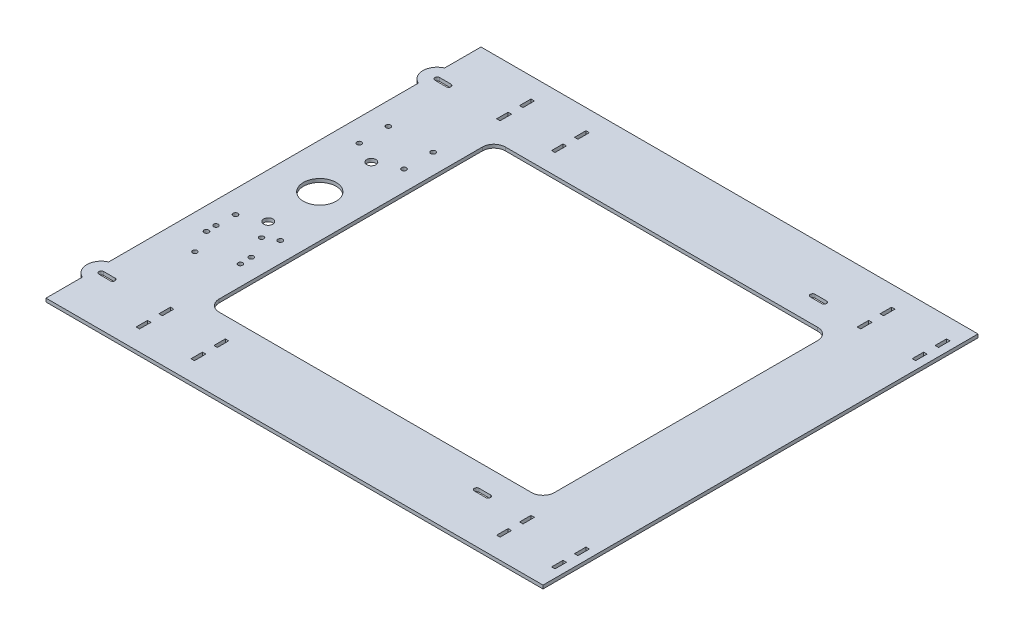
SolidWorks part; units mm, degrees
material "PC High Viscosity"
ref_plane "Front Plane" through (0, 0, 0) normal (0, 0, 1) x (1, 0, 0)
ref_plane "Top Plane" through (0, 0, 0) normal (0, 1, 0) x (1, 0, 0)
ref_plane "Right Plane" through (0, 0, 0) normal (1, 0, 0) x (0, 0, -1)
sketch "Sketch1" plane through (0, 0, 0) normal (0, 1, 0) x (1, 0, 0)
  line L1 (217.09, -190) -> (-217.09, -190)
  line L2 (217.09, -190) -> (217.09, 190)
  line L3 (217.09, 190) -> (-217.09, 190)
  line L4 (-217.09, -190) -> (-217.09, 190)
  line L5 (217.09, -190) -> (-217.09, 190) construction
  line L6 (217.09, 190) -> (-217.09, -190) construction
  point P0 (0, 0)
  dimension "D1" = 434.18
  dimension "D2" = 380
extrude "Boss-Extrude1" add sketch "Sketch1" along normal blind 3 contours L4 L3 L2 L1
sketch "Sketch2" plane through (0, 3, 0) normal (0, 1, 0) x (1, 0, 0)
  line L0 (217.09, 0) -> (-217.09, 0) construction
  line L1 (217.09, -190) -> (217.09, 190) construction
  line L2 (-217.09, 190) -> (-217.09, -190) construction
  line L4 (-97.91, -125) -> (152.09, -125)
  line L5 (-97.91, -125) -> (-97.91, 125)
  line L6 (-97.91, 125) -> (152.09, 125)
  line L7 (152.09, -125) -> (152.09, 125)
  line L8 (-97.91, -125) -> (152.09, 125) construction
  line L9 (-97.91, 125) -> (152.09, -125) construction
  line L10 (152.09, 125) -> (217.09, 125) construction
  line L11 (152.09, 125) -> (152.09, 190) construction
  line L12 (152.09, 190) -> (217.09, 190) construction
  line L13 (217.09, 125) -> (217.09, 190) construction
  point P6 (27.09, 0)
  dimension "D1" = 250
  dimension "D2" = 250
extrude "Cut-Extrude1" cut sketch "Sketch2" against normal through all
sketch "Sketch3" plane through (0, 3, 0) normal (0, 1, 0) x (1, 0, 0)
  line L0 (160.59, -152.5) -> (160.59, -162.5) construction
  line L1 (159.09, -152.5) -> (162.09, -152.5)
  line L2 (159.09, -152.5) -> (159.09, -142.5)
  line L3 (159.09, -142.5) -> (162.09, -142.5)
  line L4 (162.09, -152.5) -> (162.09, -142.5)
  line L5 (159.09, -152.5) -> (162.09, -142.5) construction
  line L6 (159.09, -142.5) -> (162.09, -152.5) construction
  line L7 (159.09, -172.5) -> (162.09, -172.5)
  line L8 (159.09, -172.5) -> (159.09, -162.5)
  line L9 (159.09, -162.5) -> (162.09, -162.5)
  line L10 (162.09, -172.5) -> (162.09, -162.5)
  line L11 (159.09, -172.5) -> (162.09, -162.5) construction
  line L12 (159.09, -162.5) -> (162.09, -172.5) construction
  line L13 (210.09, -152.5) -> (207.09, -152.5)
  line L14 (210.09, -152.5) -> (210.09, -142.5)
  line L15 (210.09, -142.5) -> (207.09, -142.5)
  line L16 (207.09, -152.5) -> (207.09, -142.5)
  line L17 (210.09, -152.5) -> (207.09, -142.5) construction
  line L18 (210.09, -142.5) -> (207.09, -152.5) construction
  line L19 (210.09, -172.5) -> (207.09, -172.5)
  line L20 (210.09, -172.5) -> (210.09, -162.5)
  line L21 (210.09, -162.5) -> (207.09, -162.5)
  line L22 (207.09, -172.5) -> (207.09, -162.5)
  line L23 (210.09, -172.5) -> (207.09, -162.5) construction
  line L24 (210.09, -162.5) -> (207.09, -172.5) construction
  line L25 (160.59, -167.5) -> (208.59, -167.5) construction
  line L26 (160.59, -167.5) -> (160.59, -147.5) construction
  line L27 (160.59, -147.5) -> (208.59, -147.5) construction
  line L28 (208.59, -167.5) -> (208.59, -147.5) construction
  line L29 (160.59, -167.5) -> (208.59, -147.5) construction
  line L30 (160.59, -147.5) -> (208.59, -167.5) construction
  line L31 (27.09, 125) -> (27.09, -125) construction
  line L32 (-130.41, 157.5) -> (184.59, 157.5) construction
  line L33 (-130.41, 157.5) -> (-130.41, -157.5) construction
  line L34 (-130.41, -157.5) -> (184.59, -157.5) construction
  line L35 (184.59, 157.5) -> (184.59, -157.5) construction
  line L36 (-130.41, 157.5) -> (184.59, -157.5) construction
  line L37 (-130.41, -157.5) -> (184.59, 157.5) construction
  line L38 (152.09, 125) -> (-97.91, 125) construction
  line L39 (-97.91, -125) -> (152.09, -125) construction
  line L40 (184.59, 0) -> (-130.41, 0) construction
  line L41 (-155.91, -142.5) -> (-152.91, -152.5) construction
  line L42 (-155.91, -152.5) -> (-152.91, -142.5) construction
  line L43 (-152.91, -152.5) -> (-152.91, -142.5)
  line L44 (-155.91, -142.5) -> (-152.91, -142.5)
  line L45 (-155.91, -152.5) -> (-155.91, -142.5)
  line L46 (-155.91, -152.5) -> (-152.91, -152.5)
  line L47 (-155.91, -162.5) -> (-152.91, -172.5) construction
  line L48 (-155.91, -172.5) -> (-152.91, -162.5) construction
  line L49 (-152.91, -172.5) -> (-152.91, -162.5)
  line L50 (-155.91, -162.5) -> (-152.91, -162.5)
  line L51 (-155.91, -172.5) -> (-155.91, -162.5)
  line L52 (-155.91, -172.5) -> (-152.91, -172.5)
  line L53 (-104.91, -162.5) -> (-107.91, -172.5) construction
  line L54 (-104.91, -172.5) -> (-107.91, -162.5) construction
  line L55 (-107.91, -172.5) -> (-107.91, -162.5)
  line L56 (-104.91, -162.5) -> (-107.91, -162.5)
  line L57 (-104.91, -172.5) -> (-104.91, -162.5)
  line L58 (-104.91, -172.5) -> (-107.91, -172.5)
  line L59 (-104.91, -142.5) -> (-107.91, -152.5) construction
  line L60 (-104.91, -152.5) -> (-107.91, -142.5) construction
  line L61 (-107.91, -152.5) -> (-107.91, -142.5)
  line L62 (-104.91, -142.5) -> (-107.91, -142.5)
  line L63 (-104.91, -152.5) -> (-104.91, -142.5)
  line L64 (-104.91, -152.5) -> (-107.91, -152.5)
  line L65 (210.09, 142.5) -> (207.09, 152.5) construction
  line L66 (210.09, 152.5) -> (207.09, 142.5) construction
  line L67 (207.09, 152.5) -> (207.09, 142.5)
  line L68 (210.09, 142.5) -> (207.09, 142.5)
  line L69 (210.09, 152.5) -> (210.09, 142.5)
  line L70 (210.09, 152.5) -> (207.09, 152.5)
  line L71 (210.09, 162.5) -> (207.09, 172.5) construction
  line L72 (210.09, 172.5) -> (207.09, 162.5) construction
  line L73 (207.09, 172.5) -> (207.09, 162.5)
  line L74 (210.09, 162.5) -> (207.09, 162.5)
  line L75 (210.09, 172.5) -> (210.09, 162.5)
  line L76 (210.09, 172.5) -> (207.09, 172.5)
  line L77 (159.09, 162.5) -> (162.09, 172.5) construction
  line L78 (159.09, 172.5) -> (162.09, 162.5) construction
  line L79 (162.09, 172.5) -> (162.09, 162.5)
  line L80 (159.09, 162.5) -> (162.09, 162.5)
  line L81 (159.09, 172.5) -> (159.09, 162.5)
  line L82 (159.09, 172.5) -> (162.09, 172.5)
  line L83 (159.09, 142.5) -> (162.09, 152.5) construction
  line L84 (159.09, 152.5) -> (162.09, 142.5) construction
  line L85 (162.09, 152.5) -> (162.09, 142.5)
  line L86 (159.09, 142.5) -> (162.09, 142.5)
  line L87 (159.09, 152.5) -> (159.09, 142.5)
  line L88 (159.09, 152.5) -> (162.09, 152.5)
  line L89 (-130.41, -157.5) -> (184.59, 157.5) construction
  line L90 (-104.91, 152.5) -> (-107.91, 142.5) construction
  line L91 (-104.91, 142.5) -> (-107.91, 152.5) construction
  line L92 (-104.91, 172.5) -> (-107.91, 162.5) construction
  line L93 (-104.91, 162.5) -> (-107.91, 172.5) construction
  line L94 (-104.91, 152.5) -> (-107.91, 152.5)
  line L95 (-104.91, 152.5) -> (-104.91, 142.5)
  line L96 (-104.91, 142.5) -> (-107.91, 142.5)
  line L97 (-107.91, 152.5) -> (-107.91, 142.5)
  line L98 (-104.91, 172.5) -> (-107.91, 172.5)
  line L99 (-104.91, 172.5) -> (-104.91, 162.5)
  line L100 (-104.91, 162.5) -> (-107.91, 162.5)
  line L101 (-107.91, 172.5) -> (-107.91, 162.5)
  line L102 (-155.91, 172.5) -> (-152.91, 162.5) construction
  line L103 (-155.91, 162.5) -> (-152.91, 172.5) construction
  line L104 (-155.91, 152.5) -> (-152.91, 142.5) construction
  line L105 (-155.91, 142.5) -> (-152.91, 152.5) construction
  line L106 (-155.91, 172.5) -> (-152.91, 172.5)
  line L107 (-155.91, 172.5) -> (-155.91, 162.5)
  line L108 (-155.91, 162.5) -> (-152.91, 162.5)
  line L109 (-152.91, 172.5) -> (-152.91, 162.5)
  line L110 (-155.91, 152.5) -> (-152.91, 152.5)
  line L111 (-155.91, 152.5) -> (-155.91, 142.5)
  line L112 (-155.91, 142.5) -> (-152.91, 142.5)
  line L113 (-152.91, 152.5) -> (-152.91, 142.5)
  line L114 (-217.09, -190) -> (217.09, -190) construction
  line L115 (152.09, -125) -> (152.09, 125) construction
  point P0 (160.59, -147.5)
  point P5 (160.59, -167.5)
  point P10 (208.59, -147.5)
  point P15 (208.59, -167.5)
  point P20 (184.59, -157.5)
  point P27 (27.09, 0)
  point P44 (-154.41, -147.5)
  point P49 (-154.41, -167.5)
  point P54 (-106.41, -167.5)
  point P59 (-106.41, -147.5)
  point P64 (208.59, 147.5)
  point P69 (208.59, 167.5)
  point P74 (160.59, 167.5)
  point P79 (160.59, 147.5)
  point P88 (-106.41, 147.5)
  point P89 (-106.41, 167.5)
  point P98 (-154.41, 167.5)
  point P99 (-154.41, 147.5)
  dimension "D1" = 3
  dimension "D2" = 45
  dimension "D3" = 10
  dimension "D4" = 32.5
  dimension "D5" = 32.5
extrude "Cut-Extrude2" cut sketch "Sketch3" against normal through all
sketch "Sketch6" plane through (0, 3, 0) normal (0, 1, 0) x (1, 0, 0)
  line L0 (-197.475, 10) -> (-158.345, 10) construction
  line L1 (-97.91, 125) -> (-97.91, -125) construction
  line L2 (-158.345, -44.0505) -> (-197.475, -44.0505) construction
  line L3 (-168.6822, -50.1326) -> (-158.0266, -79.2438) construction
  line L4 (-168.6822, -50.1326) -> (-197.7934, -60.7882) construction
  line L5 (-197.7934, -60.7882) -> (-187.1378, -89.8994) construction
  line L6 (-158.0266, -79.2438) -> (-187.1378, -89.8994) construction
  line L7 (-168.6822, -50.1326) -> (-187.1378, -89.8994) construction
  line L8 (-197.7934, -60.7882) -> (-158.0266, -79.2438) construction
  line L9 (-158.345, -44.0505) -> (-158.345, 64.0505) construction
  line L10 (-158.345, 64.0505) -> (-197.475, 64.0505) construction
  line L11 (-197.475, -44.0505) -> (-197.475, 64.0505) construction
  line L12 (-158.345, -44.0505) -> (-197.475, 64.0505) construction
  line L13 (-158.345, 64.0505) -> (-197.475, -44.0505) construction
  line L14 (-197.475, 64.0505) -> (-158.345, 64.0505) construction
  line L15 (-197.475, 64.0505) -> (-197.475, 89.4505) construction
  line L16 (-197.475, 89.4505) -> (-158.345, 89.4505) construction
  line L17 (-158.345, 64.0505) -> (-158.345, 89.4505) construction
  line L18 (-217.09, 10) -> (-97.91, 10) construction
  line L20 (-217.09, 190) -> (-217.09, -190) construction
  line L21 (-97.91, 125) -> (-97.91, -125) construction
  circle A0 centre (-177.91, 10) radius 14.2875
  circle A1 centre (-197.7934, -60.7882) radius 2
  circle A2 centre (-187.1378, -89.8994) radius 2
  circle A3 centre (-158.0266, -79.2438) radius 2
  circle A4 centre (-168.6822, -50.1326) radius 2
  circle A5 centre (-158.345, 64.0505) radius 2.0833
  circle A6 centre (-197.475, 64.0505) radius 2.0833
  circle A7 centre (-197.475, -44.0505) radius 2.0833
  circle A8 centre (-158.345, -44.0505) radius 2.0833
  circle A9 centre (-197.475, 89.4505) radius 2.0833
  circle A10 centre (-158.345, 89.4505) radius 2.0833
  circle A11 centre (-158.345, -69.4505) radius 2.0833
  circle A12 centre (-197.475, -69.4505) radius 2.0833
  circle A13 centre (-177.91, -35) radius 4
  circle A14 centre (-177.91, 55) radius 4
  point P6 (-177.91, -70.016)
  dimension "D1" = 28.575
  dimension "D2" = 80
  dimension "D3" = 4
  dimension "D9" = 4.1667
  dimension "D11" = 8
  dimension "D12" = 90
  dimension "D4" = 31
  dimension "D5" = 80.016
  dimension "D6" = 10
  dimension "D7" = 108.101
  dimension "D8" = 39.13
  dimension "D10" = 25.4
extrude "Cut-Extrude3" cut sketch "Sketch6" against normal through all
sketch "Sketch7" plane through (0, 3, 0) normal (0, 1, 0) x (1, 0, 0)
  line L0 (-97.91, -125) -> (152.09, -125) construction
  line L1 (-57.5273, -125) -> (-140.8107, -125)
  line L2 (-57.5273, -125) -> (-57.5273, 125)
  line L3 (-57.5273, 125) -> (-140.8107, 125)
  line L4 (-140.8107, -125) -> (-140.8107, 125)
  line L5 (152.09, 125) -> (-97.91, 125) construction
extrude "Cut-Extrude4" cut sketch "Sketch7" against normal through all
fillet "Fillet1" radius 10 4 edges at (152.09, 1.5, 125) (152.09, 1.5, -125) (-140.8107, 1.5, 125) (-140.8107, 1.5, -125)
sketch "Sketch8" plane through (0, 3, 0) normal (0, 1, 0) x (1, 0, 0)
  line L0 (-217.09, 190) -> (-217.09, -190) construction
  line L1 (-212.09, 146.75) -> (115.91, 146.75) construction
  line L2 (-212.09, 146.75) -> (-212.09, -146.75) construction
  line L3 (-212.09, -146.75) -> (115.91, -146.75) construction
  line L4 (115.91, 146.75) -> (115.91, -146.75) construction
  line L5 (-212.09, 146.75) -> (115.91, -146.75) construction
  line L6 (-212.09, -146.75) -> (115.91, 146.75) construction
  line L7 (-212.09, 146.75) -> (-202.09, 146.75) construction
  line L8 (-212.09, 148.805) -> (-202.09, 148.805)
  line L9 (-212.09, 144.695) -> (-202.09, 144.695)
  line L10 (-212.09, -146.75) -> (-202.09, -146.75) construction
  line L11 (-212.09, -144.695) -> (-202.09, -144.695)
  line L12 (-212.09, -148.805) -> (-202.09, -148.805)
  line L13 (115.91, -146.75) -> (125.91, -146.75) construction
  line L14 (115.91, -144.695) -> (125.91, -144.695)
  line L15 (115.91, -148.805) -> (125.91, -148.805)
  line L16 (115.91, 146.75) -> (125.91, 146.75) construction
  line L17 (115.91, 148.805) -> (125.91, 148.805)
  line L18 (115.91, 144.695) -> (125.91, 144.695)
  arc A0 (-212.09, 148.805) -> (-212.09, 144.695) centre (-212.09, 146.75) ccw
  arc A1 (-202.09, 144.695) -> (-202.09, 148.805) centre (-202.09, 146.75) ccw
  arc A2 (-212.09, -144.695) -> (-212.09, -148.805) centre (-212.09, -146.75) ccw
  arc A3 (-202.09, -148.805) -> (-202.09, -144.695) centre (-202.09, -146.75) ccw
  arc A4 (115.91, -144.695) -> (115.91, -148.805) centre (115.91, -146.75) ccw
  arc A5 (125.91, -148.805) -> (125.91, -144.695) centre (125.91, -146.75) ccw
  arc A6 (115.91, 148.805) -> (115.91, 144.695) centre (115.91, 146.75) ccw
  arc A7 (125.91, 144.695) -> (125.91, 148.805) centre (125.91, 146.75) ccw
  point P0 (-48.09, 0)
  point P8 (-207.09, 146.75)
  point P14 (-207.09, -146.75)
  point P20 (120.91, -146.75)
  point P26 (120.91, 146.75)
  dimension "D4" = 2.055
  dimension "D1" = 328
  dimension "D2" = 293.5
  dimension "D3" = 5
  dimension "D5" = 10
extrude "Cut-Extrude5" cut sketch "Sketch8" against normal through all
sketch "Sketch9" plane through (0, 3, 0) normal (0, 1, 0) x (1, 0, 0)
  line L0 (-202.09, -144.695) -> (-212.09, -144.695) construction
  line L3 (-212.09, -148.805) -> (-202.09, -148.805) construction
  line L4 (-202.09, -144.695) -> (-212.09, -144.695)
  line L5 (-212.09, -148.805) -> (-202.09, -148.805)
  line L6 (-202.09, 148.805) -> (-212.09, 148.805) construction
  line L7 (-212.09, 144.695) -> (-202.09, 144.695) construction
  line L8 (-202.09, 148.805) -> (-212.09, 148.805)
  line L9 (-212.09, 144.695) -> (-202.09, 144.695)
  circle A0 centre (-212.09, 146.75) radius 12.5
  circle A1 centre (-212.09, -146.75) radius 12.5
  arc A3 (-212.09, -144.695) -> (-212.09, -148.805) centre (-212.09, -146.75) ccw construction
  arc A4 (-202.09, -148.805) -> (-202.09, -144.695) centre (-202.09, -146.75) ccw construction
  arc A5 (-202.09, -148.805) -> (-202.09, -144.695) centre (-202.09, -146.75) ccw
  arc A6 (-212.09, -144.695) -> (-212.09, -148.805) centre (-212.09, -146.75) ccw
  arc A7 (-202.09, 144.695) -> (-202.09, 148.805) centre (-202.09, 146.75) ccw construction
  arc A8 (-212.09, 148.805) -> (-212.09, 144.695) centre (-212.09, 146.75) ccw construction
  arc A9 (-202.09, 144.695) -> (-202.09, 148.805) centre (-202.09, 146.75) ccw
  arc A10 (-212.09, 148.805) -> (-212.09, 144.695) centre (-212.09, 146.75) ccw
  dimension "D1" = 25
extrude "Boss-Extrude2" add sketch "Sketch9" against normal up to surface (3 mm away) contours A0 A10 L8 A9 L9 | A1 A6 L4 A5 L5 up to face at (120.91, 0, -146.75)
equation "\"case_width\"= 16.7in"
equation "\"case_depth\"= 12.6in"
equation "\"D1@Sketch1\"=\"case_width\" + 10mm"
equation "\"pulley_pitch_diam\"= 12.73mm"
equation "\"pulley_total_width\"= 16mm"
equation "\"pulley_total_diam\"= 16mm"
equation "\"belt_width\"= 6mm"
equation "\"material_thickness\"= 3mm"
equation "\"shaft_diam\"= 8mm"
equation "\"bearing_od\"= 22mm"
equation "\"bearing_thickness\"= 7mm"
